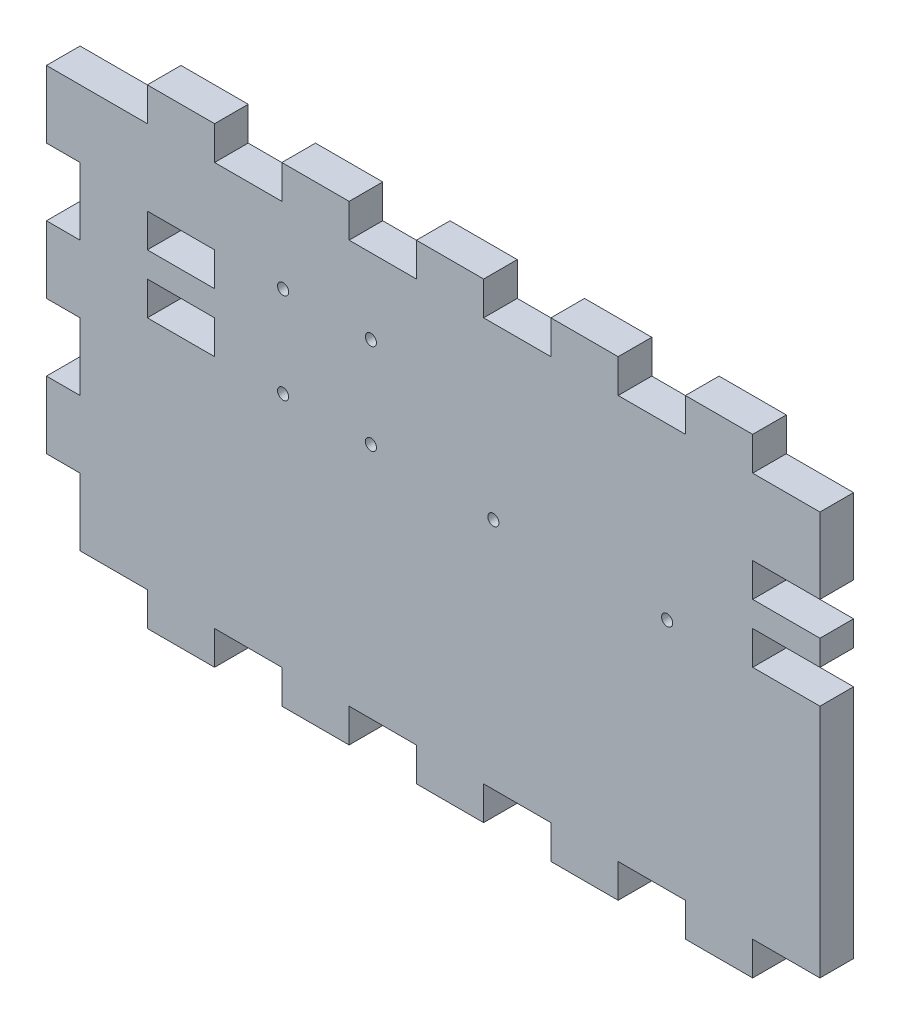
SolidWorks part; units mm, degrees
ref_plane "Front Plane" through (0, 0, 0) normal (0, 0, 1) x (1, 0, 0)
ref_plane "Top Plane" through (0, 0, 0) normal (0, 1, 0) x (1, 0, 0)
ref_plane "Right Plane" through (0, 0, 0) normal (1, 0, 0) x (0, 0, -1)
sketch "Sketch1" plane through (0, 0, 0) normal (0, 0, 1) x (1, 0, 0)
  line L1 (-139.7, -76.2) -> (139.7, -76.2)
  line L2 (-139.7, -76.2) -> (-139.7, 76.2)
  line L3 (-139.7, 76.2) -> (139.7, 76.2)
  line L4 (139.7, -76.2) -> (139.7, 76.2)
  line L5 (-139.7, -76.2) -> (139.7, 76.2) construction
  line L6 (-139.7, 76.2) -> (139.7, -76.2) construction
  point P0 (0, 0)
  dimension "D1" = 279.4
  dimension "D2" = 152.4
extrude "Boss-Extrude1" add sketch "Sketch1" along normal blind 12.7
sketch "Sketch2" plane through (0, -76.2, 0) normal (0, -1, 0) x (1, 0, 0)
  line L0 (-139.7, 0) -> (139.7, 0) construction
  line L1 (-114.3, 0) -> (-88.9, 0)
  line L2 (-114.3, 0) -> (-114.3, 12.7)
  line L3 (-114.3, 12.7) -> (-88.9, 12.7)
  line L4 (-88.9, 0) -> (-88.9, 12.7)
  line L5 (-139.7, 12.7) -> (139.7, 12.7) construction
  line L6 (-139.7, 12.7) -> (-139.7, 0) construction
  point P10 (-139.7, 6.35)
  dimension "D1" = 25.4
  dimension "D2" = 25.4
extrude "Boss-Extrude2" add sketch "Sketch2" along normal blind 12.7
pattern_linear "LPattern1" count 5 spacing 50.8 along (1, 0, 0) of "Boss-Extrude2"
mirror "Mirror1" about plane through (0, 0, 0) normal (0, 1, 0) of "LPattern1", "Boss-Extrude2"
sketch "Sketch3" plane through (-139.7, 0, 0) normal (-1, 0, 0) x (0, 0, 1)
  line L0 (0, 76.2) -> (0, -76.2) construction
  line L1 (12.7, 76.2) -> (0, 76.2)
  line L2 (12.7, 76.2) -> (12.7, 50.8)
  line L3 (12.7, 50.8) -> (0, 50.8)
  line L4 (0, 76.2) -> (0, 50.8)
  dimension "D1" = 25.4
extrude "Boss-Extrude3" add sketch "Sketch3" along normal blind 12.7
pattern_linear "LPattern2" count 3 spacing 50.8 along (0, -1, 0) of "Boss-Extrude3"
sketch "Sketch4" plane through (0, 0, 0) normal (0, 0, -1) x (-1, 0, 0)
  line L1 (-139.7, 12.7) -> (-114.3, 12.7)
  line L2 (-139.7, 12.7) -> (-139.7, 25.4)
  line L3 (-139.7, 25.4) -> (-114.3, 25.4)
  line L4 (-114.3, 12.7) -> (-114.3, 25.4)
  line L5 (-114.3, -76.2) -> (-139.7, -76.2) construction
  line L6 (-139.7, -76.2) -> (-139.7, 76.2) construction
  dimension "D1" = 25.4
  dimension "D2" = 12.7
  dimension "D4" = 88.9
extrude "Cut-Extrude1" cut sketch "Sketch4" against normal through all
pattern_linear "LPattern3" count 2 spacing 228.6 along (-1, 0, 0) of "Cut-Extrude1"
sketch "Sketch5" plane through (0, 0, 12.7) normal (0, 0, 1) x (1, 0, 0)
  line L0 (-139.7, -76.2) -> (-114.3, -76.2) construction
  line L1 (-88.9, 47.625) -> (-114.3, 47.625)
  line L2 (-88.9, 47.625) -> (-88.9, 34.925)
  line L3 (-88.9, 34.925) -> (-114.3, 34.925)
  line L4 (-114.3, 47.625) -> (-114.3, 34.925)
  line L8 (-114.3, 12.7) -> (-114.3, 25.4) construction
  dimension "D1" = 25.4
  dimension "D2" = 12.7
  dimension "D3" = 123.825
extrude "Cut-Extrude2" cut sketch "Sketch5" against normal through all
pattern_linear "LPattern4" count 2 spacing 228.6 along (1, 0, 0) of "Cut-Extrude2"
sketch "Sketch6" plane through (0, 0, 0) normal (0, 0, -1) x (-1, 0, 0)
  circle A0 centre (-81.9861, 12) radius 2.1 construction
  circle A1 centre (-81.9861, 12) radius 2.1
  circle A2 centre (-16.3789, 12) radius 2.1 construction
  circle A3 centre (-16.3789, 12) radius 2.1
  circle A4 centre (63.02, 13.5088) radius 2.1 construction
  circle A5 centre (63.02, 13.5088) radius 2.1
  circle A6 centre (29.87, 47.77) radius 2.1 construction
  circle A7 centre (29.87, 47.77) radius 2.1
  circle A8 centre (63.02, 47.77) radius 2.1 construction
  circle A9 centre (63.02, 47.77) radius 2.1
  circle A10 centre (29.87, 13.5088) radius 2.1 construction
  circle A11 centre (29.87, 13.5088) radius 2.1
extrude "Cut-Extrude3" cut sketch "Sketch6" against normal through all
